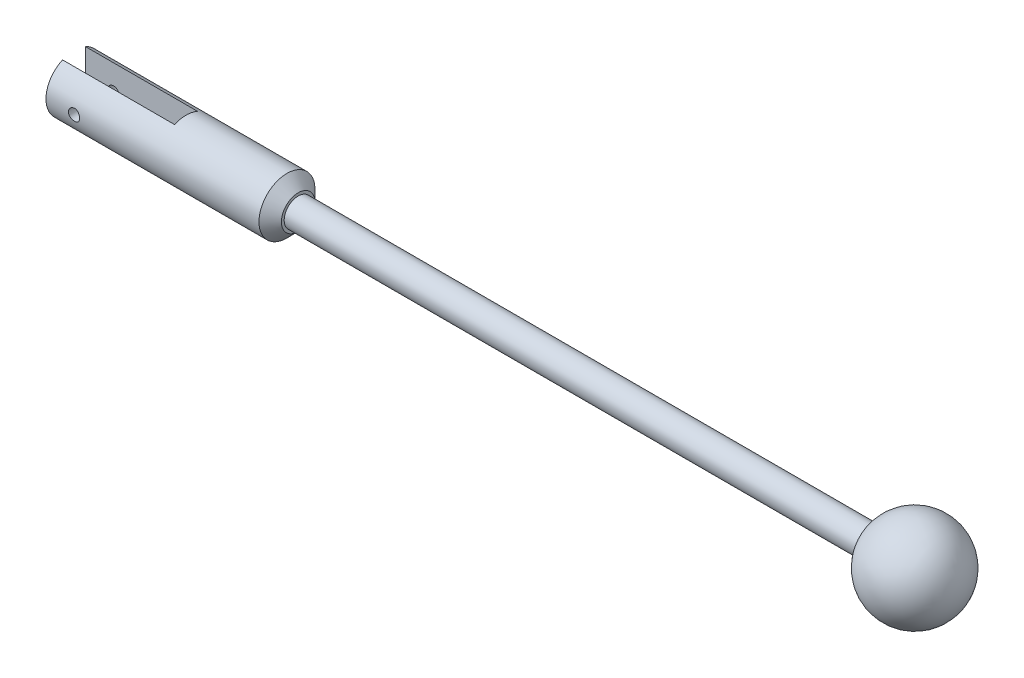
SolidWorks part; units mm, degrees
ref_plane "Front Plane" through (0, 0, 0) normal (0, 0, 1) x (1, 0, 0)
ref_plane "Top Plane" through (0, 0, 0) normal (0, 1, 0) x (1, 0, 0)
ref_plane "Right Plane" through (0, 0, 0) normal (1, 0, 0) x (0, 0, -1)
sketch "Sketch1" plane through (0, 0, 0) normal (0, 1, 0) x (1, 0, 0)
  line L0 (-37.5, 0) -> (37.5, 0)
  line L1 (-37.5, -1.25) -> (37.5, -1.25)
  line L2 (-37.5, -1.25) -> (-37.5, 1.25)
  line L3 (-37.5, 1.25) -> (37.5, 1.25)
  line L4 (37.5, -1.25) -> (37.5, 1.25)
  line L5 (-37.5, -1.25) -> (37.5, 1.25) construction
  line L6 (-37.5, 1.25) -> (37.5, -1.25) construction
  point P0 (0, 0)
  dimension "D1" = 75
  dimension "D2" = 2.5
revolve "Revolve2" add sketch "Sketch1" angle 360 about L0
sketch "Sketch2" plane through (-37.5, 0, 0) normal (-1, 0, 0) x (0, 0, 1)
  circle A0 centre (0, 0) radius 2.5
  dimension "D1" = 5
extrude "Boss-Extrude1" add sketch "Sketch2" against normal blind 20
sketch "Sketch3" plane through (-37.5, 0, 0) normal (-1, 0, 0) x (0, 0, 1)
  line L1 (-1.025, -2.5) -> (1.025, -2.5)
  line L2 (-1.025, -2.5) -> (-1.025, 2.5)
  line L3 (-1.025, 2.5) -> (1.025, 2.5)
  line L4 (1.025, -2.5) -> (1.025, 2.5)
  line L5 (-1.025, -2.5) -> (1.025, 2.5) construction
  line L6 (-1.025, 2.5) -> (1.025, -2.5) construction
  circle A0 centre (0, 0) radius 2.5 construction
  point P0 (0, 0)
  dimension "D1" = 2.05
extrude "Cut-Extrude1" cut sketch "Sketch3" against normal blind 10 and the other way through all
chamfer "Chamfer1" distance 1 angle 45 1 edges at (-17.5, 0, 2.5)
sketch "Sketch4" plane through (0, 0, -1.025) normal (0, 0, 1) x (1, 0, 0)
  line L0 (-37.5, 2.2802) -> (-37.5, -2.2802) construction
  circle A0 centre (-35, 0) radius 0.5
  dimension "D1" = 1
  dimension "D2" = 2.5
extrude "Cut-Extrude2" cut sketch "Sketch4" against normal through all both and the other way through all
sketch "Sketch5" plane through (37.5, 0, 0) normal (1, 0, 0) x (0, 0, -1)
  line L0 (-4, 0) -> (4, 0)
  circle A0 centre (0, 0) radius 4
  dimension "D1" = 8
revolve "Revolve3" add sketch "Sketch5" angle 360 about L0
